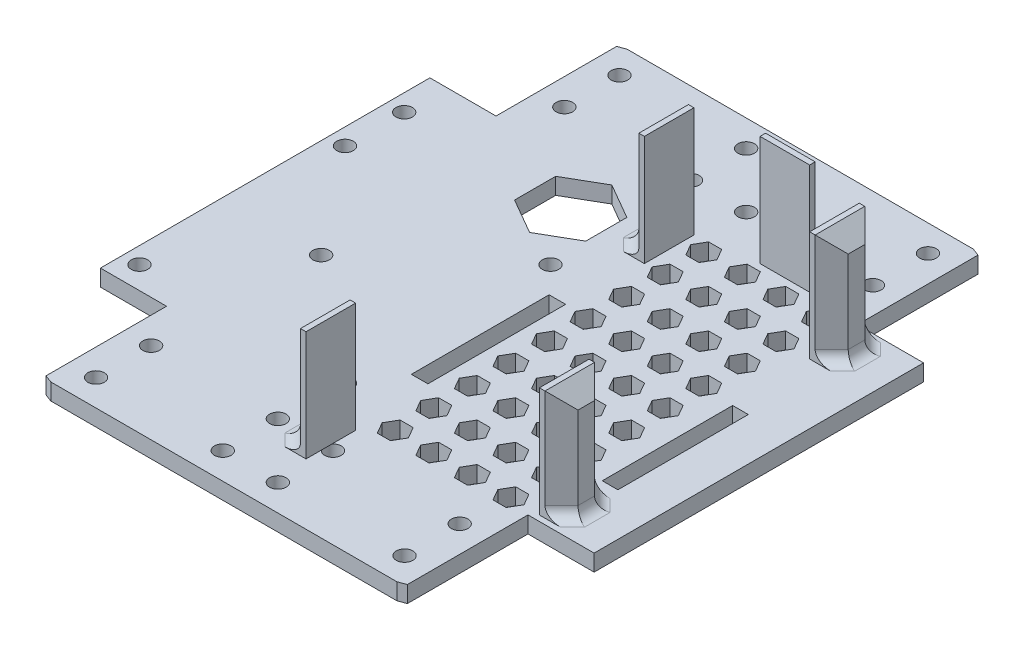
SolidWorks part; units mm, degrees
ref_plane "Front Plane" through (0, 0, 0) normal (0, 0, 1) x (1, 0, 0)
ref_plane "Top Plane" through (0, 0, 0) normal (0, 1, 0) x (1, 0, 0)
ref_plane "Right Plane" through (0, 0, 0) normal (1, 0, 0) x (0, 0, -1)
sketch "Sketch1" plane through (0, 0, 0) normal (0, 1, 0) x (1, 0, 0)
  line L0 (-33, -43.3177) -> (-33, -21.5) construction
  line L1 (-33, -21.5) -> (-45, -21.5) construction
  line L2 (-45, -21.5) -> (-45, 38.7) construction
  line L3 (-45, 38.5) -> (-32.8, 38.5) construction
  line L4 (-33, -43.3177) -> (-31.4513, -43.9) construction
  line L5 (-31.4513, -43.9) -> (31.4513, -43.9) construction
  line L6 (31.4513, -43.9) -> (33, -43.3177) construction
  line L7 (33, -43.3177) -> (33, -21.5) construction
  line L8 (33, -21.5) -> (45, -21.5) construction
  line L9 (45, -21.5) -> (45, 38.7) construction
  line L10 (-32.8, -43.1792) -> (-32.8, -21.3)
  line L11 (-32.8, -21.3) -> (-44.8, -21.3)
  line L12 (-44.8, -21.3) -> (-44.8, 38.5)
  line L13 (32.8, 38.5) -> (45, 38.5) construction
  line L14 (44.8, -21.3) -> (44.8, 38.5)
  line L15 (32.8, -21.3) -> (44.8, -21.3)
  line L16 (32.8, -43.1792) -> (32.8, -21.3)
  line L17 (31.4149, -43.7) -> (32.8, -43.1792)
  line L18 (-31.4149, -43.7) -> (31.4149, -43.7)
  line L19 (-32.8, -43.1792) -> (-31.4149, -43.7)
  line L20 (-31.4513, 61.1) -> (31.4513, 61.1) construction
  line L21 (31.4513, 61.1) -> (33, 60.5177) construction
  line L22 (33, 60.5177) -> (33, 38.7) construction
  line L23 (33, 38.7) -> (45, 38.7) construction
  line L24 (45, 38.7) -> (45, -21.5) construction
  line L25 (45, -21.5) -> (33, -21.5) construction
  line L26 (33, -21.5) -> (33, -43.3177) construction
  line L27 (33, -43.3177) -> (31.4513, -43.9) construction
  line L28 (31.4513, -43.9) -> (-31.4513, -43.9) construction
  line L29 (-31.4513, -43.9) -> (-33, -43.3177) construction
  line L30 (-33, -43.3177) -> (-33, -21.5) construction
  line L31 (-33, -21.5) -> (-45, -21.5) construction
  line L32 (-45, -21.5) -> (-45, 38.7) construction
  line L33 (-45, 38.7) -> (-33, 38.7) construction
  line L34 (-33, 38.7) -> (-33, 60.5177) construction
  line L35 (-33, 60.5177) -> (-31.4513, 61.1) construction
  line L36 (-44.8, 38.5) -> (-32.8, 38.5)
  line L37 (-32.8, 38.5) -> (-32.8, 60.3792)
  line L38 (-32.8, 60.3792) -> (-31.4149, 60.9)
  line L39 (-31.4149, 60.9) -> (31.4149, 60.9)
  line L40 (31.4149, 60.9) -> (32.8, 60.3792)
  line L41 (32.8, 60.3792) -> (32.8, 38.5)
  line L42 (32.8, 38.5) -> (44.8, 38.5)
  line L43 (-45, 43.9) -> (45, 43.9) construction
  line L44 (-44.8, 43.7) -> (44.8, 43.7) construction
  line L45 (-44.8, -21.3) -> (-44.8, 43.7) construction
  line L46 (-45, -21.5) -> (-45, 43.9) construction
  line L47 (-44.8, 8.6) -> (44.8, 8.6) construction
  line L49 (44.8, -21.3) -> (44.8, 43.7) construction
  line L50 (45, -21.5) -> (45, 43.9) construction
  circle A0 centre (-28, -28.9) radius 1.5
  circle A1 centre (-28, -38.9) radius 1.5
  circle A2 centre (-5, -28.9) radius 1.5
  circle A3 centre (5, -28.9) radius 1.5
  circle A4 centre (-5, -38.9) radius 1.5
  circle A5 centre (5, -38.9) radius 1.5
  circle A6 centre (28, -28.9) radius 1.5
  circle A7 centre (28, -38.9) radius 1.5
  circle A8 centre (-28, -28.9) radius 1.3 construction
  circle A9 centre (-28, -38.9) radius 1.3 construction
  circle A10 centre (-5, -28.9) radius 1.3 construction
  circle A11 centre (5, -28.9) radius 1.3 construction
  circle A12 centre (-5, -38.9) radius 1.3 construction
  circle A13 centre (5, -38.9) radius 1.3 construction
  circle A14 centre (28, -28.9) radius 1.3 construction
  circle A15 centre (28, -38.9) radius 1.3 construction
  circle A16 centre (28, 56.1) radius 1.3 construction
  circle A17 centre (28, 46.1) radius 1.3 construction
  circle A18 centre (5, 56.1) radius 1.3 construction
  circle A19 centre (-5, 56.1) radius 1.3 construction
  circle A20 centre (5, 46.1) radius 1.3 construction
  circle A21 centre (-5, 46.1) radius 1.3 construction
  circle A22 centre (-28, 56.1) radius 1.3 construction
  circle A23 centre (-28, 46.1) radius 1.3 construction
  circle A24 centre (28, 56.1) radius 1.5
  circle A25 centre (28, 46.1) radius 1.5
  circle A26 centre (5, 56.1) radius 1.5
  circle A27 centre (-5, 56.1) radius 1.5
  circle A28 centre (5, 46.1) radius 1.5
  circle A29 centre (-5, 46.1) radius 1.5
  circle A30 centre (-28, 56.1) radius 1.5
  circle A31 centre (-28, 46.1) radius 1.5
  dimension "D1" = 0.2
  dimension "D2" = 0.2
extrude "Boss-Extrude1" add sketch "Sketch1" along normal blind 3
sketch "Sketch2" plane through (0, 3, 0) normal (0, 1, 0) x (1, 0, 0)
  circle A2 centre (-41.8, -17.2116) radius 1.5
  circle A3 centre (-4.5, -17.2116) radius 1.5
  circle A4 centre (-41.8, 20.0884) radius 1.5
  circle A5 centre (-4.5, 20.0884) radius 1.5
extrude "Cut-Extrude1" cut sketch "Sketch2" against normal blind 10
sketch "Sketch3" plane through (0, 3, 0) normal (0, 1, 0) x (1, 0, 0)
  line L0 (-4.5, -17.2116) -> (-41.8, -17.2116) construction
  line L1 (-41.8, -17.2116) -> (-41.8, 20.0884) construction
  line L2 (-41.8, 20.0884) -> (-4.5, 20.0884) construction
  line L3 (-4.5, 20.0884) -> (-4.5, -17.2116) construction
  line L4 (-4.5, -17.2116) -> (-41.8, 20.0884) construction
  line L13 (-11.45, 23.2473) -> (-4.9895, 26.9773)
  line L14 (-4.9895, 26.9773) -> (-4.9895, 34.4373)
  line L15 (-4.9895, 34.4373) -> (-11.45, 38.1673)
  line L16 (-11.45, 38.1673) -> (-17.9105, 34.4373)
  line L17 (-17.9105, 34.4373) -> (-17.9105, 26.9773)
  line L18 (-17.9105, 26.9773) -> (-11.45, 23.2473)
  circle A1 centre (-11.45, 30.7073) radius 6.4605 construction
  point P8 (-11.45, 30.7073)
  point P21 (-38.26, 40.53)
extrude "Cut-Extrude2" cut sketch "Sketch3" against normal blind 10
sketch "Sketch4" plane through (0, 3, 0) normal (0, 1, 0) x (1, 0, 0)
  line L0 (1.8633, 33.2624) -> (35.8633, 33.2624) construction
  line L1 (3.1766, 39.2354) -> (33.2529, 39.2354) construction
  line L2 (37.8633, 37.7624) -> (33.8633, 37.7624)
  line L3 (37.8633, 37.7624) -> (37.8633, 28.7624)
  line L4 (37.8633, 28.7624) -> (33.8633, 28.7624)
  line L5 (1.8633, 33.2624) -> (1.8633, -28.1501) construction
  line L6 (33.8633, 37.7624) -> (33.8633, 28.7624)
  line L7 (33.2529, -21.3) -> (33.2529, 39.2354) construction
  line L8 (-0.1367, 37.7624) -> (3.8633, 37.7624)
  line L9 (-0.1367, 37.7624) -> (-0.1367, 28.7624)
  line L10 (-0.1367, 28.7624) -> (3.8633, 28.7624)
  line L11 (3.8633, 37.7624) -> (3.8633, 28.7624)
  line L12 (-0.1367, 37.7624) -> (3.8633, 28.7624) construction
  line L13 (-0.1367, 28.7624) -> (3.8633, 37.7624) construction
  line L14 (37.8633, 37.7624) -> (33.8633, 28.7624) construction
  line L15 (37.8633, 28.7624) -> (33.8633, 37.7624) construction
  line L16 (14.3633, 43.2624) -> (23.3633, 43.2624)
  line L17 (14.3633, 43.2624) -> (14.3633, 39.2624)
  line L18 (14.3633, 39.2624) -> (23.3633, 39.2624)
  line L19 (23.3633, 43.2624) -> (23.3633, 39.2624)
  line L20 (14.3633, 43.2624) -> (23.3633, 39.2624) construction
  line L21 (14.3633, 39.2624) -> (23.3633, 43.2624) construction
  line L22 (18.8633, 33.2624) -> (18.8633, 41.2624) construction
  line L23 (18.8633, 33.2624) -> (18.8633, -38.4732) construction
  line L24 (18.8633, -15.7757) -> (35.8633, -15.7757) construction
  line L25 (37.8633, -11.2757) -> (33.8633, -11.2757)
  line L26 (37.8633, -11.2757) -> (37.8633, -20.2757)
  line L27 (37.8633, -20.2757) -> (33.8633, -20.2757)
  line L28 (33.8633, -11.2757) -> (33.8633, -20.2757)
  line L29 (37.8633, -11.2757) -> (33.8633, -20.2757) construction
  line L30 (37.8633, -20.2757) -> (33.8633, -11.2757) construction
  line L31 (-0.1367, -32.6501) -> (3.8633, -32.6501)
  line L32 (14.3633, -36.4732) -> (14.3633, -40.4732) construction
  line L33 (14.3633, -36.4732) -> (23.3633, -36.4732) construction
  line L34 (23.3633, -36.4732) -> (23.3633, -40.4732) construction
  line L35 (14.3633, -40.4732) -> (23.3633, -40.4732) construction
  line L36 (14.3633, -36.4732) -> (23.3633, -40.4732) construction
  line L37 (23.3633, -36.4732) -> (14.3633, -40.4732) construction
  line L38 (-0.1367, -32.6501) -> (-0.1367, -23.6501)
  line L39 (-0.1367, -23.6501) -> (3.8633, -23.6501)
  line L40 (3.8633, -32.6501) -> (3.8633, -23.6501)
  line L41 (-0.1367, -32.6501) -> (3.8633, -23.6501) construction
  line L42 (-0.1367, -23.6501) -> (3.8633, -32.6501) construction
  line L43 (1.8633, -28.1501) -> (18.8633, -28.1501) construction
  point P0 (35.8633, 33.2624)
  point P2 (1.8633, 33.2624)
  point P15 (18.8633, 41.2624)
  dimension "D1" = 9
  dimension "D2" = 4
  dimension "D3" = 4
  dimension "D4" = 9
  dimension "D5" = 4
  dimension "D6" = 9
  dimension "D7" = 34
  dimension "D8" = 8
extrude "Boss-Extrude2" add sketch "Sketch4" along normal blind 20
sketch "Sketch5" plane through (0, 3, 0) normal (0, 1, 0) x (1, 0, 0)
  line L0 (18.8633, 39.2624) -> (18.8633, -36.4732) construction
  line L1 (14.3633, 39.2624) -> (23.3633, 39.2624) construction
  line L4 (6.2714, 33.8784) -> (8.6558, 33.8784)
  line L5 (8.6558, 33.8784) -> (9.848, 35.9433)
  line L6 (9.848, 35.9433) -> (8.6558, 38.0082)
  line L7 (8.6558, 38.0082) -> (6.2714, 38.0082)
  line L8 (6.2714, 38.0082) -> (5.0793, 35.9433)
  line L9 (5.0793, 35.9433) -> (6.2714, 33.8784)
  line L10 (13.2714, 33.8784) -> (15.6558, 33.8784)
  line L11 (15.6558, 33.8784) -> (16.848, 35.9433)
  line L12 (16.848, 35.9433) -> (15.6558, 38.0082)
  line L13 (15.6558, 38.0082) -> (13.2714, 38.0082)
  line L14 (13.2714, 38.0082) -> (12.0793, 35.9433)
  line L15 (12.0793, 35.9433) -> (13.2714, 33.8784)
  line L16 (20.2714, 33.8784) -> (22.6558, 33.8784)
  line L17 (22.6558, 33.8784) -> (23.848, 35.9433)
  line L18 (23.848, 35.9433) -> (22.6558, 38.0082)
  line L19 (22.6558, 38.0082) -> (20.2714, 38.0082)
  line L20 (20.2714, 38.0082) -> (19.0793, 35.9433)
  line L21 (19.0793, 35.9433) -> (20.2714, 33.8784)
  line L22 (27.2714, 33.8784) -> (29.6558, 33.8784)
  line L23 (29.6558, 33.8784) -> (30.848, 35.9433)
  line L24 (30.848, 35.9433) -> (29.6558, 38.0082)
  line L25 (29.6558, 38.0082) -> (27.2714, 38.0082)
  line L26 (27.2714, 38.0082) -> (26.0793, 35.9433)
  line L27 (26.0793, 35.9433) -> (27.2714, 33.8784)
  line L28 (13.2714, 26.8784) -> (15.6558, 26.8784)
  line L29 (15.6558, 26.8784) -> (16.848, 28.9433)
  line L30 (16.848, 28.9433) -> (15.6558, 31.0082)
  line L31 (15.6558, 31.0082) -> (13.2714, 31.0082)
  line L32 (13.2714, 31.0082) -> (12.0793, 28.9433)
  line L33 (12.0793, 28.9433) -> (13.2714, 26.8784)
  line L34 (20.2714, 26.8784) -> (22.6558, 26.8784)
  line L35 (22.6558, 26.8784) -> (23.848, 28.9433)
  line L36 (23.848, 28.9433) -> (22.6558, 31.0082)
  line L37 (22.6558, 31.0082) -> (20.2714, 31.0082)
  line L38 (20.2714, 31.0082) -> (19.0793, 28.9433)
  line L39 (19.0793, 28.9433) -> (20.2714, 26.8784)
  line L40 (27.2714, 26.8784) -> (29.6558, 26.8784)
  line L41 (29.6558, 26.8784) -> (30.848, 28.9433)
  line L42 (30.848, 28.9433) -> (29.6558, 31.0082)
  line L43 (29.6558, 31.0082) -> (27.2714, 31.0082)
  line L44 (27.2714, 31.0082) -> (26.0793, 28.9433)
  line L45 (26.0793, 28.9433) -> (27.2714, 26.8784)
  line L46 (13.2714, 19.8784) -> (15.6558, 19.8784)
  line L47 (15.6558, 19.8784) -> (16.848, 21.9433)
  line L48 (16.848, 21.9433) -> (15.6558, 24.0082)
  line L49 (15.6558, 24.0082) -> (13.2714, 24.0082)
  line L50 (13.2714, 24.0082) -> (12.0793, 21.9433)
  line L51 (12.0793, 21.9433) -> (13.2714, 19.8784)
  line L52 (20.2714, 19.8784) -> (22.6558, 19.8784)
  line L53 (22.6558, 19.8784) -> (23.848, 21.9433)
  line L54 (23.848, 21.9433) -> (22.6558, 24.0082)
  line L55 (22.6558, 24.0082) -> (20.2714, 24.0082)
  line L56 (20.2714, 24.0082) -> (19.0793, 21.9433)
  line L57 (19.0793, 21.9433) -> (20.2714, 19.8784)
  line L58 (27.2714, 19.8784) -> (29.6558, 19.8784)
  line L59 (29.6558, 19.8784) -> (30.848, 21.9433)
  line L60 (30.848, 21.9433) -> (29.6558, 24.0082)
  line L61 (29.6558, 24.0082) -> (27.2714, 24.0082)
  line L62 (27.2714, 24.0082) -> (26.0793, 21.9433)
  line L63 (26.0793, 21.9433) -> (27.2714, 19.8784)
  line L64 (13.2714, 12.8784) -> (15.6558, 12.8784)
  line L65 (15.6558, 12.8784) -> (16.848, 14.9433)
  line L66 (16.848, 14.9433) -> (15.6558, 17.0082)
  line L67 (15.6558, 17.0082) -> (13.2714, 17.0082)
  line L68 (13.2714, 17.0082) -> (12.0793, 14.9433)
  line L69 (12.0793, 14.9433) -> (13.2714, 12.8784)
  line L70 (20.2714, 12.8784) -> (22.6558, 12.8784)
  line L71 (22.6558, 12.8784) -> (23.848, 14.9433)
  line L72 (23.848, 14.9433) -> (22.6558, 17.0082)
  line L73 (22.6558, 17.0082) -> (20.2714, 17.0082)
  line L74 (20.2714, 17.0082) -> (19.0793, 14.9433)
  line L75 (19.0793, 14.9433) -> (20.2714, 12.8784)
  line L76 (27.2714, 12.8784) -> (29.6558, 12.8784)
  line L77 (29.6558, 12.8784) -> (30.848, 14.9433)
  line L78 (30.848, 14.9433) -> (29.6558, 17.0082)
  line L79 (29.6558, 17.0082) -> (27.2714, 17.0082)
  line L80 (27.2714, 17.0082) -> (26.0793, 14.9433)
  line L81 (26.0793, 14.9433) -> (27.2714, 12.8784)
  line L82 (13.2714, 5.8784) -> (15.6558, 5.8784)
  line L83 (15.6558, 5.8784) -> (16.848, 7.9433)
  line L84 (16.848, 7.9433) -> (15.6558, 10.0082)
  line L85 (15.6558, 10.0082) -> (13.2714, 10.0082)
  line L86 (13.2714, 10.0082) -> (12.0793, 7.9433)
  line L87 (12.0793, 7.9433) -> (13.2714, 5.8784)
  line L88 (20.2714, 5.8784) -> (22.6558, 5.8784)
  line L89 (22.6558, 5.8784) -> (23.848, 7.9433)
  line L90 (23.848, 7.9433) -> (22.6558, 10.0082)
  line L91 (22.6558, 10.0082) -> (20.2714, 10.0082)
  line L92 (20.2714, 10.0082) -> (19.0793, 7.9433)
  line L93 (19.0793, 7.9433) -> (20.2714, 5.8784)
  line L94 (27.2714, 5.8784) -> (29.6558, 5.8784)
  line L95 (29.6558, 5.8784) -> (30.848, 7.9433)
  line L96 (30.848, 7.9433) -> (29.6558, 10.0082)
  line L97 (29.6558, 10.0082) -> (27.2714, 10.0082)
  line L98 (27.2714, 10.0082) -> (26.0793, 7.9433)
  line L99 (26.0793, 7.9433) -> (27.2714, 5.8784)
  line L100 (13.2714, -1.1216) -> (15.6558, -1.1216)
  line L101 (15.6558, -1.1216) -> (16.848, 0.9433)
  line L102 (16.848, 0.9433) -> (15.6558, 3.0082)
  line L103 (15.6558, 3.0082) -> (13.2714, 3.0082)
  line L104 (13.2714, 3.0082) -> (12.0793, 0.9433)
  line L105 (12.0793, 0.9433) -> (13.2714, -1.1216)
  line L106 (20.2714, -1.1216) -> (22.6558, -1.1216)
  line L107 (22.6558, -1.1216) -> (23.848, 0.9433)
  line L108 (23.848, 0.9433) -> (22.6558, 3.0082)
  line L109 (22.6558, 3.0082) -> (20.2714, 3.0082)
  line L110 (20.2714, 3.0082) -> (19.0793, 0.9433)
  line L111 (19.0793, 0.9433) -> (20.2714, -1.1216)
  line L112 (27.2714, -1.1216) -> (29.6558, -1.1216)
  line L113 (29.6558, -1.1216) -> (30.848, 0.9433)
  line L114 (30.848, 0.9433) -> (29.6558, 3.0082)
  line L115 (29.6558, 3.0082) -> (27.2714, 3.0082)
  line L116 (27.2714, 3.0082) -> (26.0793, 0.9433)
  line L117 (26.0793, 0.9433) -> (27.2714, -1.1216)
  line L118 (13.2714, -8.1216) -> (15.6558, -8.1216)
  line L119 (15.6558, -8.1216) -> (16.848, -6.0567)
  line L120 (16.848, -6.0567) -> (15.6558, -3.9918)
  line L121 (15.6558, -3.9918) -> (13.2714, -3.9918)
  line L122 (13.2714, -3.9918) -> (12.0793, -6.0567)
  line L123 (12.0793, -6.0567) -> (13.2714, -8.1216)
  line L124 (20.2714, -8.1216) -> (22.6558, -8.1216)
  line L125 (22.6558, -8.1216) -> (23.848, -6.0567)
  line L126 (23.848, -6.0567) -> (22.6558, -3.9918)
  line L127 (22.6558, -3.9918) -> (20.2714, -3.9918)
  line L128 (20.2714, -3.9918) -> (19.0793, -6.0567)
  line L129 (19.0793, -6.0567) -> (20.2714, -8.1216)
  line L130 (27.2714, -8.1216) -> (29.6558, -8.1216)
  line L131 (29.6558, -8.1216) -> (30.848, -6.0567)
  line L132 (30.848, -6.0567) -> (29.6558, -3.9918)
  line L133 (29.6558, -3.9918) -> (27.2714, -3.9918)
  line L134 (27.2714, -3.9918) -> (26.0793, -6.0567)
  line L135 (26.0793, -6.0567) -> (27.2714, -8.1216)
  line L136 (13.2714, -15.1216) -> (15.6558, -15.1216)
  line L137 (15.6558, -15.1216) -> (16.848, -13.0567)
  line L138 (16.848, -13.0567) -> (15.6558, -10.9918)
  line L139 (15.6558, -10.9918) -> (13.2714, -10.9918)
  line L140 (13.2714, -10.9918) -> (12.0793, -13.0567)
  line L141 (12.0793, -13.0567) -> (13.2714, -15.1216)
  line L142 (20.2714, -15.1216) -> (22.6558, -15.1216)
  line L143 (22.6558, -15.1216) -> (23.848, -13.0567)
  line L144 (23.848, -13.0567) -> (22.6558, -10.9918)
  line L145 (22.6558, -10.9918) -> (20.2714, -10.9918)
  line L146 (20.2714, -10.9918) -> (19.0793, -13.0567)
  line L147 (19.0793, -13.0567) -> (20.2714, -15.1216)
  line L148 (27.2714, -15.1216) -> (29.6558, -15.1216)
  line L149 (29.6558, -15.1216) -> (30.848, -13.0567)
  line L150 (30.848, -13.0567) -> (29.6558, -10.9918)
  line L151 (29.6558, -10.9918) -> (27.2714, -10.9918)
  line L152 (27.2714, -10.9918) -> (26.0793, -13.0567)
  line L153 (26.0793, -13.0567) -> (27.2714, -15.1216)
  line L154 (13.2714, -22.1216) -> (15.6558, -22.1216)
  line L155 (15.6558, -22.1216) -> (16.848, -20.0567)
  line L156 (16.848, -20.0567) -> (15.6558, -17.9918)
  line L157 (15.6558, -17.9918) -> (13.2714, -17.9918)
  line L158 (13.2714, -17.9918) -> (12.0793, -20.0567)
  line L159 (12.0793, -20.0567) -> (13.2714, -22.1216)
  line L160 (20.2714, -22.1216) -> (22.6558, -22.1216)
  line L161 (22.6558, -22.1216) -> (23.848, -20.0567)
  line L162 (23.848, -20.0567) -> (22.6558, -17.9918)
  line L163 (22.6558, -17.9918) -> (20.2714, -17.9918)
  line L164 (20.2714, -17.9918) -> (19.0793, -20.0567)
  line L165 (19.0793, -20.0567) -> (20.2714, -22.1216)
  line L166 (27.2714, -22.1216) -> (29.6558, -22.1216)
  line L167 (29.6558, -22.1216) -> (30.848, -20.0567)
  line L168 (30.848, -20.0567) -> (29.6558, -17.9918)
  line L169 (29.6558, -17.9918) -> (27.2714, -17.9918)
  line L170 (27.2714, -17.9918) -> (26.0793, -20.0567)
  line L171 (26.0793, -20.0567) -> (27.2714, -22.1216)
  line L172 (6.2714, 26.8784) -> (8.6558, 26.8784)
  line L173 (8.6558, 26.8784) -> (9.848, 28.9433)
  line L174 (9.848, 28.9433) -> (8.6558, 31.0082)
  line L175 (8.6558, 31.0082) -> (6.2714, 31.0082)
  line L176 (6.2714, 31.0082) -> (5.0793, 28.9433)
  line L177 (5.0793, 28.9433) -> (6.2714, 26.8784)
  line L178 (6.2714, 19.8784) -> (8.6558, 19.8784)
  line L179 (8.6558, 19.8784) -> (9.848, 21.9433)
  line L180 (9.848, 21.9433) -> (8.6558, 24.0082)
  line L181 (8.6558, 24.0082) -> (6.2714, 24.0082)
  line L182 (6.2714, 24.0082) -> (5.0793, 21.9433)
  line L183 (5.0793, 21.9433) -> (6.2714, 19.8784)
  line L184 (6.2714, 12.8784) -> (8.6558, 12.8784)
  line L185 (8.6558, 12.8784) -> (9.848, 14.9433)
  line L186 (9.848, 14.9433) -> (8.6558, 17.0082)
  line L187 (8.6558, 17.0082) -> (6.2714, 17.0082)
  line L188 (6.2714, 17.0082) -> (5.0793, 14.9433)
  line L189 (5.0793, 14.9433) -> (6.2714, 12.8784)
  line L190 (6.2714, 5.8784) -> (8.6558, 5.8784)
  line L191 (8.6558, 5.8784) -> (9.848, 7.9433)
  line L192 (9.848, 7.9433) -> (8.6558, 10.0082)
  line L193 (8.6558, 10.0082) -> (6.2714, 10.0082)
  line L194 (6.2714, 10.0082) -> (5.0793, 7.9433)
  line L195 (5.0793, 7.9433) -> (6.2714, 5.8784)
  line L196 (6.2714, -1.1216) -> (8.6558, -1.1216)
  line L197 (8.6558, -1.1216) -> (9.848, 0.9433)
  line L198 (9.848, 0.9433) -> (8.6558, 3.0082)
  line L199 (8.6558, 3.0082) -> (6.2714, 3.0082)
  line L200 (6.2714, 3.0082) -> (5.0793, 0.9433)
  line L201 (5.0793, 0.9433) -> (6.2714, -1.1216)
  line L202 (6.2714, -8.1216) -> (8.6558, -8.1216)
  line L203 (8.6558, -8.1216) -> (9.848, -6.0567)
  line L204 (9.848, -6.0567) -> (8.6558, -3.9918)
  line L205 (8.6558, -3.9918) -> (6.2714, -3.9918)
  line L206 (6.2714, -3.9918) -> (5.0793, -6.0567)
  line L207 (5.0793, -6.0567) -> (6.2714, -8.1216)
  line L208 (6.2714, -15.1216) -> (8.6558, -15.1216)
  line L209 (8.6558, -15.1216) -> (9.848, -13.0567)
  line L210 (9.848, -13.0567) -> (8.6558, -10.9918)
  line L211 (8.6558, -10.9918) -> (6.2714, -10.9918)
  line L212 (6.2714, -10.9918) -> (5.0793, -13.0567)
  line L213 (5.0793, -13.0567) -> (6.2714, -15.1216)
  line L214 (6.2714, -22.1216) -> (8.6558, -22.1216)
  line L215 (8.6558, -22.1216) -> (9.848, -20.0567)
  line L216 (9.848, -20.0567) -> (8.6558, -17.9918)
  line L217 (8.6558, -17.9918) -> (6.2714, -17.9918)
  line L218 (6.2714, -17.9918) -> (5.0793, -20.0567)
  line L219 (5.0793, -20.0567) -> (6.2714, -22.1216)
  circle A0 centre (7.4636, 35.9433) radius 2.0649 construction
  circle A1 centre (14.4636, 35.9433) radius 2.0649 construction
  circle A2 centre (21.4636, 35.9433) radius 2.0649 construction
  circle A3 centre (28.4636, 35.9433) radius 2.0649 construction
  circle A4 centre (14.4636, 28.9433) radius 2.0649 construction
  circle A5 centre (21.4636, 28.9433) radius 2.0649 construction
  circle A6 centre (28.4636, 28.9433) radius 2.0649 construction
  circle A7 centre (14.4636, 21.9433) radius 2.0649 construction
  circle A8 centre (21.4636, 21.9433) radius 2.0649 construction
  circle A9 centre (28.4636, 21.9433) radius 2.0649 construction
  circle A10 centre (14.4636, 14.9433) radius 2.0649 construction
  circle A11 centre (21.4636, 14.9433) radius 2.0649 construction
  circle A12 centre (28.4636, 14.9433) radius 2.0649 construction
  circle A13 centre (14.4636, 7.9433) radius 2.0649 construction
  circle A14 centre (21.4636, 7.9433) radius 2.0649 construction
  circle A15 centre (28.4636, 7.9433) radius 2.0649 construction
  circle A16 centre (14.4636, 0.9433) radius 2.0649 construction
  circle A17 centre (21.4636, 0.9433) radius 2.0649 construction
  circle A18 centre (28.4636, 0.9433) radius 2.0649 construction
  circle A19 centre (14.4636, -6.0567) radius 2.0649 construction
  circle A20 centre (21.4636, -6.0567) radius 2.0649 construction
  circle A21 centre (28.4636, -6.0567) radius 2.0649 construction
  circle A22 centre (14.4636, -13.0567) radius 2.0649 construction
  circle A23 centre (21.4636, -13.0567) radius 2.0649 construction
  circle A24 centre (28.4636, -13.0567) radius 2.0649 construction
  circle A25 centre (14.4636, -20.0567) radius 2.0649 construction
  circle A26 centre (21.4636, -20.0567) radius 2.0649 construction
  circle A27 centre (28.4636, -20.0567) radius 2.0649 construction
  circle A28 centre (7.4636, 28.9433) radius 2.0649 construction
  circle A29 centre (7.4636, 21.9433) radius 2.0649 construction
  circle A30 centre (7.4636, 14.9433) radius 2.0649 construction
  circle A31 centre (7.4636, 7.9433) radius 2.0649 construction
  circle A32 centre (7.4636, 0.9433) radius 2.0649 construction
  circle A33 centre (7.4636, -6.0567) radius 2.0649 construction
  circle A34 centre (7.4636, -13.0567) radius 2.0649 construction
  circle A35 centre (7.4636, -20.0567) radius 2.0649 construction
  point P7 (0, 0)
  dimension "D1" = 4
  dimension "D2" = 9
extrude "Cut-Extrude3" cut sketch "Sketch5" against normal blind 5
chamfer "Chamfer1" distance 3 angle 45 5 edges at (-0.1367, 23, 28.1501) (37.8633, 23, 15.7757) (37.8633, 23, -33.2624) (18.8633, 23, -43.2624) (-0.1367, 23, -33.2624)
chamfer "Chamfer2" distance 3 angle 45 10 edges at (-0.1367, 11.5, 32.6501) (-0.1367, 11.5, 23.6501) (37.8633, 11.5, 11.2757) (37.8633, 11.5, 20.2757) (37.8633, 11.5, -28.7624) (37.8633, 11.5, -37.7624) (23.3633, 11.5, -43.2624) (14.3633, 11.5, -43.2624) (-0.1367, 11.5, -37.7624) (-0.1367, 11.5, -28.7624)
fillet "Fillet1" radius 2 15 edges at (-0.1367, 3, 28.1501) (1.3633, 3, 25.1501) (1.3633, 3, 31.1501) (36.3633, 3, 18.7757) (37.8633, 3, 15.7757) (36.3633, 3, 12.7757) (36.3633, 3, -30.2624) (37.8633, 3, -33.2624) (36.3633, 3, -36.2624) (18.8633, 3, -43.2624) (21.8633, 3, -41.7624) (15.8633, 3, -41.7624) (-0.1367, 3, -33.2624) (1.3633, 3, -36.2624) (1.3633, 3, -30.2624)
sketch "Sketch6" plane through (0, 3, 0) normal (0, 1, 0) x (1, 0, 0)
  line L0 (34.1758, -9.1966) -> (37.0162, -9.1966)
  line L1 (0.1177, -9.7835) -> (3.1177, -9.7835)
  line L2 (0.1177, -9.7835) -> (0.1177, 15.2165)
  line L3 (0.1177, 15.2165) -> (3.1177, 15.2165)
  line L4 (3.1177, -9.7835) -> (3.1177, 15.2165)
  line L5 (0.1177, -9.7835) -> (3.1177, 15.2165) construction
  line L6 (0.1177, 15.2165) -> (3.1177, -9.7835) construction
  line L7 (34.1758, -9.1966) -> (34.1758, 14.4728)
  line L8 (34.1758, 14.4728) -> (37.0162, 14.4728)
  line L9 (37.0162, -9.1966) -> (37.0162, 14.4728)
  line L10 (34.1758, -9.1966) -> (37.0162, 14.4728) construction
  line L11 (34.1758, 14.4728) -> (37.0162, -9.1966) construction
  point P0 (1.6177, 2.7165)
  point P6 (35.596, 2.6381)
  dimension "D1" = 3
  dimension "D2" = 25
extrude "Cut-Extrude4" cut sketch "Sketch6" against normal blind 5
sketch "Sketch7" plane through (0, 0, 0) normal (0, -1, 0) x (-1, 0, 0)
  circle A0 centre (26.8057, 0.765) radius 1.5
  circle A1 centre (41.7257, 30.755) radius 1.5
extrude "Cut-Extrude5" cut sketch "Sketch7" against normal blind 10
